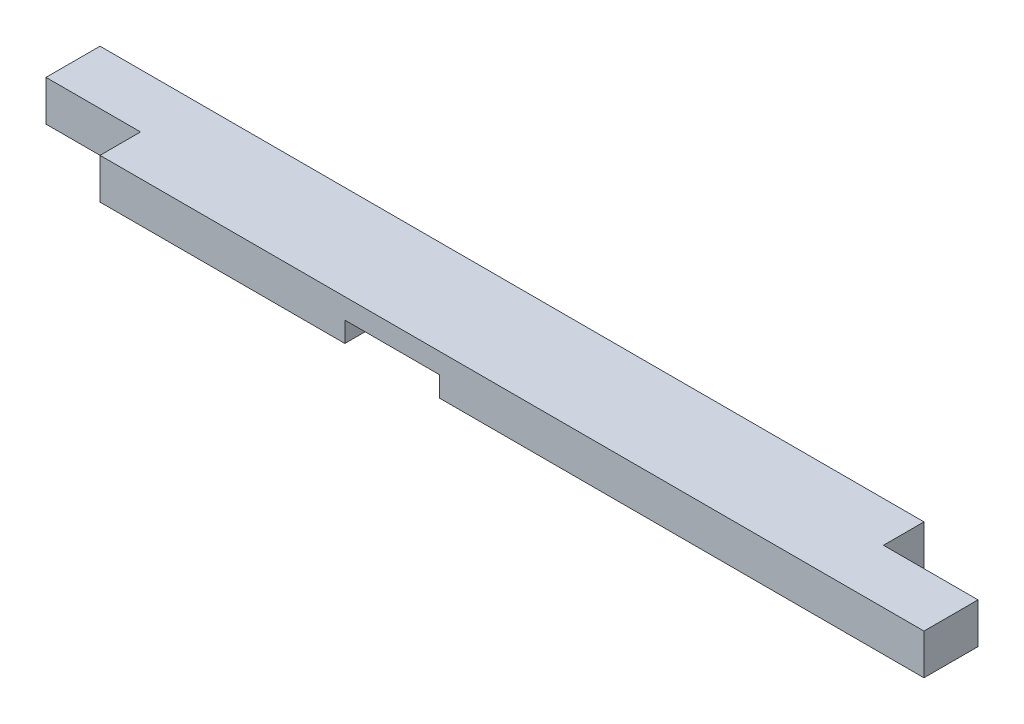
SolidWorks part; units mm, degrees
material "Pine"
ref_plane "Front Plane" through (0, 0, 0) normal (0, 0, 1) x (1, 0, 0)
ref_plane "Top Plane" through (0, 0, 0) normal (0, 1, 0) x (1, 0, 0)
ref_plane "Right Plane" through (0, 0, 0) normal (1, 0, 0) x (0, 0, -1)
sketch "Sketch1" plane through (0, 0, 0) normal (0, 1, 0) x (1, 0, 0)
  line L1 (0, 0) -> (863.6, 0)
  line L2 (0, 0) -> (0, 88.9)
  line L3 (0, 88.9) -> (863.6, 88.9)
  line L4 (863.6, 0) -> (863.6, 88.9)
  dimension "D1" = 88.9
  dimension "D2" = 863.6
extrude "Boss-Extrude1" add sketch "Sketch1" along normal blind 38.1
sketch "Sketch2" plane through (0, 0, 0) normal (0, -1, 0) x (1, 0, 0)
  line L0 (0, 0) -> (863.6, 0) construction
  line L1 (319.1002, 0) -> (408.0002, 0)
  line L2 (319.1002, 0) -> (319.1002, -88.9)
  line L3 (319.1002, -88.9) -> (408.0002, -88.9)
  line L4 (408.0002, 0) -> (408.0002, -88.9)
  line L5 (863.6, -88.9) -> (0, -88.9) construction
  dimension "D1" = 319.1002
  dimension "D2" = 88.9
extrude "Cut-Extrude1" cut sketch "Sketch2" against normal blind 19.05
sketch "Sketch3" plane through (0, 38.1, 0) normal (0, 1, 0) x (1, 0, 0)
  line L1 (0, 0) -> (88.9, 0)
  line L2 (0, 0) -> (0, 38.1)
  line L3 (0, 38.1) -> (88.9, 38.1)
  line L4 (88.9, 0) -> (88.9, 38.1)
  dimension "D1" = 38.1
  dimension "D2" = 88.9
extrude "Cut-Extrude2" cut sketch "Sketch3" against normal through all
sketch "Sketch4" plane through (0, 38.1, 0) normal (0, 1, 0) x (1, 0, 0)
  line L1 (863.6, 88.9) -> (774.7, 88.9)
  line L2 (863.6, 88.9) -> (863.6, 50.8)
  line L3 (863.6, 50.8) -> (774.7, 50.8)
  line L4 (774.7, 88.9) -> (774.7, 50.8)
  dimension "D1" = 50.8
  dimension "D2" = 774.7
extrude "Cut-Extrude3" cut sketch "Sketch4" against normal through all
